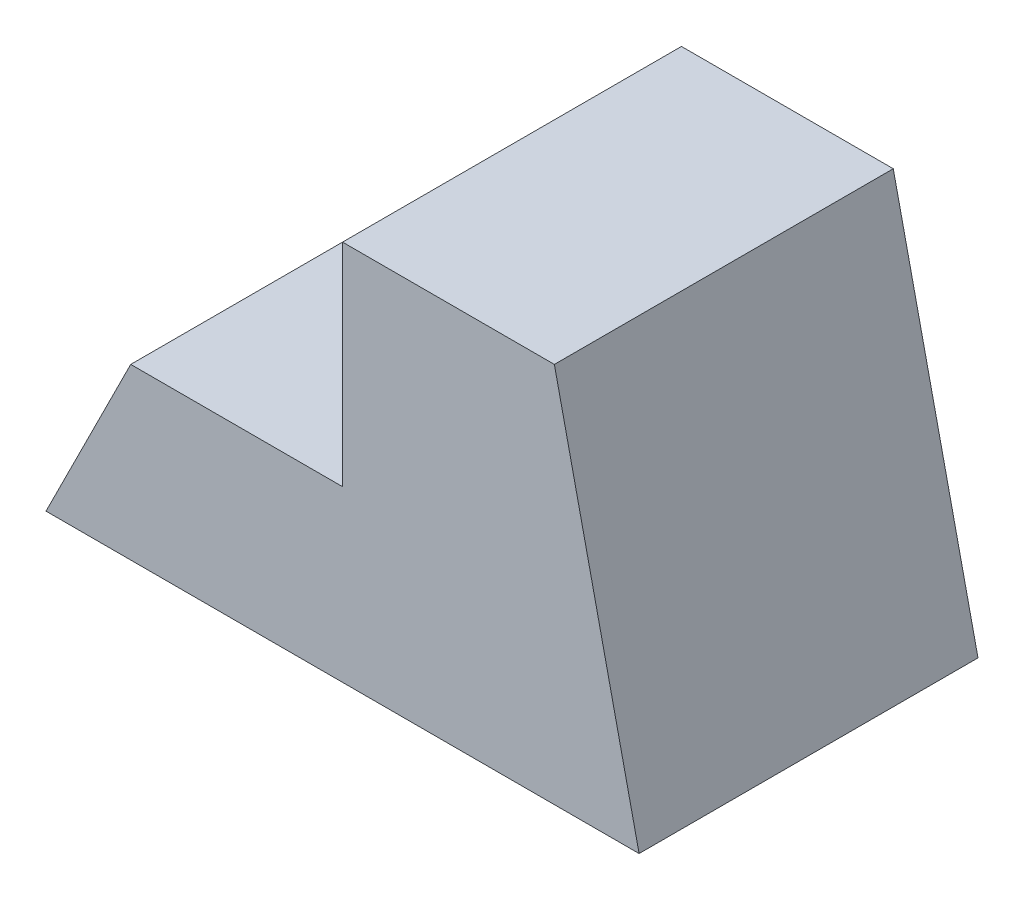
SolidWorks part; units mm, degrees
ref_plane "Front Plane" through (0, 0, 0) normal (0, 0, 1) x (1, 0, 0)
ref_plane "Top Plane" through (0, 0, 0) normal (0, 1, 0) x (1, 0, 0)
ref_plane "Right Plane" through (0, 0, 0) normal (1, 0, 0) x (0, 0, -1)
sketch "Sketch2" plane through (0, 0, 0) normal (0, 0, 1) x (1, 0, 0)
  line L0 (0, 0) -> (70, 0)
  line L1 (70, 0) -> (60, 45)
  line L2 (60, 45) -> (35, 45)
  line L3 (35, 45) -> (35, 20)
  line L4 (35, 20) -> (10, 20)
  line L5 (10, 20) -> (0, 0)
  dimension "D1" = 70
  dimension "D2" = 45
  dimension "D3" = 10
  dimension "D4" = 10
  dimension "D5" = 20
  dimension "D6" = 25
extrude "Boss-Extrude1" add sketch "Sketch2" along normal blind 40
